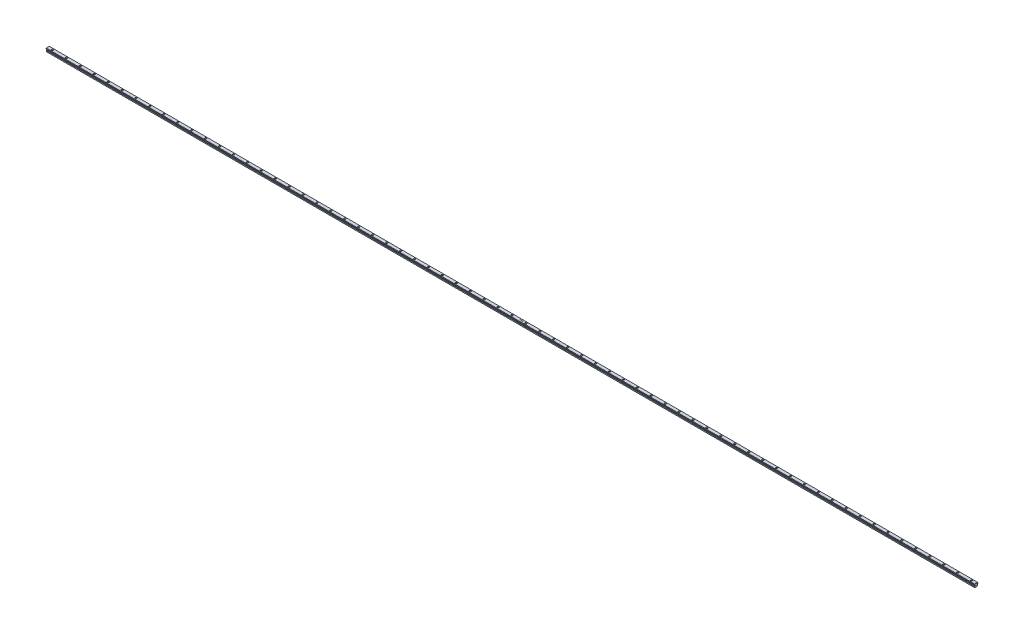
SolidWorks part; units mm, degrees
ref_plane "Front Plane" through (0, 0, 0) normal (0, 0, 1) x (1, 0, 0)
ref_plane "Top Plane" through (0, 0, 0) normal (0, 1, 0) x (1, 0, 0)
ref_plane "Right Plane" through (0, 0, 0) normal (1, 0, 0) x (0, 0, -1)
sketch "Sketch1" plane through (0, 0, 0) normal (1, 0, 0) x (0, 0, -1)
  line L0 (0, 44.5417) -> (0, -63.6994) construction
  line L1 (-6.5, 31.4906) -> (6.5, 31.4906)
  line L2 (6.5, 31.4906) -> (7.7587, 30.232)
  line L3 (7.7587, 30.232) -> (7.7587, 28.232)
  line L4 (7.7587, 28.232) -> (4.7747, 26.3274)
  line L5 (4.7747, 26.3274) -> (4.7747, 24.3274)
  line L6 (4.7747, 24.3274) -> (6.5, 22.602)
  line L7 (6.5, 22.602) -> (6.5, 18.002)
  line L8 (-6.5, 22.602) -> (-6.5, 18.002)
  line L9 (-4.7747, 24.3274) -> (-6.5, 22.602)
  line L10 (-4.7747, 26.3274) -> (-4.7747, 24.3274)
  line L11 (-7.7587, 28.232) -> (-4.7747, 26.3274)
  line L12 (-7.7587, 30.232) -> (-7.7587, 28.232)
  line L13 (-6.5, 31.4906) -> (-7.7587, 30.232)
  line L14 (-6.5, 18.002) -> (6.5, 18.002)
  dimension "D2" = 6.5
  dimension "D3" = 1.78
  dimension "D4" = 2
  dimension "D5" = 3.54
  dimension "D6" = 2
  dimension "D7" = 2.44
  dimension "D8" = 4.6
  dimension "D13" = 13
extrude "Boss-Extrude1" add sketch "Sketch1" along normal mid plane 4000
sketch "Sketch2" plane through (0, 31.4906, 0) normal (0, 1, 0) x (1, 0, 0)
  line L0 (2000, 6.5) -> (2000, -6.5) construction
  circle A0 centre (1980, 0) radius 3.75
  dimension "D1" = 7.5
  dimension "D2" = 20
extrude "Cut-Extrude1" cut sketch "Sketch2" against normal blind 5.3
sketch "Sketch3" plane through (0, 26.1906, 0) normal (0, 1, 0) x (1, 0, 0)
  circle A0 centre (1980, 0) radius 2.25
  dimension "D1" = 4.5
extrude "Cut-Extrude2" cut sketch "Sketch3" against normal through all
chamfer "Chamfer1" distance 1 angle 45 1 edges at (2000, 31.4906, 0)
pattern_linear "LPattern1" count 67 spacing 60 along (-1, 0, 0) of "Cut-Extrude1", "Cut-Extrude2"
sketch "Sketch4" plane through (0, 31.4906, 0) normal (0, 1, 0) x (1, 0, 0)
  line L0 (-2000, 6.5) -> (-2000, -6.5) construction
  text T0 "SHN 15 A"
  point P3 (-2000, 0)
extrude "Cut-Extrude3" cut sketch "Sketch4" against normal blind 2
